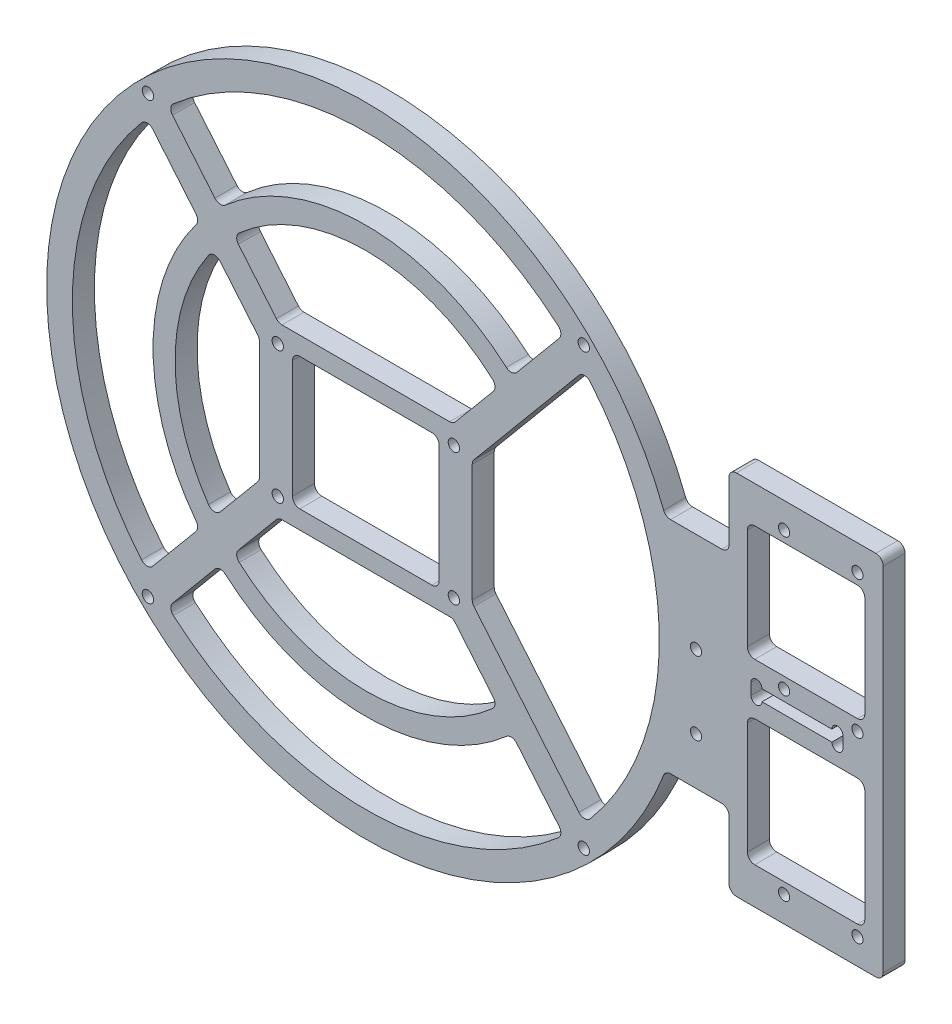
SolidWorks part; units mm, degrees
material "Thornel Mat VMA"
ref_plane "前视基准面" through (0, 0, 0) normal (0, 0, 1) x (1, 0, 0)
ref_plane "上视基准面" through (0, 0, 0) normal (0, 1, 0) x (1, 0, 0)
ref_plane "右视基准面" through (0, 0, 0) normal (1, 0, 0) x (0, 0, -1)
other "Configuration Table"
sketch "草图1" plane through (0, 0, 0) normal (0, 0, 1) x (1, 0, 0)
  line L1 (-24, -18) -> (24, -18) construction
  line L2 (-24, -18) -> (-24, 18) construction
  line L3 (-24, 18) -> (24, 18) construction
  line L4 (24, -18) -> (24, 18) construction
  line L5 (-24, -18) -> (24, 18) construction
  line L6 (-24, 18) -> (24, -18) construction
  circle A0 centre (24, 18) radius 1.55
  circle A1 centre (-24, 18) radius 1.55
  circle A2 centre (-24, -18) radius 1.55
  circle A3 centre (24, -18) radius 1.55
  circle A4 centre (0, 0) radius 87
  point P0 (0, 0)
  dimension "D3" = 3.1
  dimension "D4" = 174
  dimension "D1" = 48
  dimension "D2" = 36
extrude "凸台-拉伸1" add sketch "草图1" along normal blind 6
sketch "草图2" plane through (0, 0, 6) normal (0, 0, 1) x (1, 0, 0)
  line L0 (0, 87) -> (0, 0) construction
  line L1 (0, 0) -> (59.397, 59.397) construction
  circle A0 centre (0, 0) radius 84 construction
  circle A1 centre (0, 0) radius 87 construction
  circle A2 centre (59.397, 59.397) radius 1.55
  circle A3 centre (59.397, -59.397) radius 1.55
  circle A4 centre (-59.397, -59.397) radius 1.55
  circle A5 centre (-59.397, 59.397) radius 1.55
  point P17 (0, 0)
  dimension "D1" = 3
  dimension "D3" = 3.1
  dimension "D2" = 45
  dimension "D4" = 4
extrude "切除-拉伸1" cut sketch "草图2" against normal blind 40
sketch "草图3" plane through (0, 0, 6) normal (0, 0, 1) x (1, 0, 0)
  line L0 (0, 0) -> (87, 0) construction
  line L1 (37, -30) -> (137, -30)
  line L2 (37, -30) -> (37, 30)
  line L3 (37, 30) -> (137, 30)
  line L4 (137, -30) -> (137, 30)
  line L5 (37, -30) -> (137, 30) construction
  line L6 (37, 30) -> (137, -30) construction
  circle A0 centre (0, 0) radius 87 construction
  point P0 (87, 0)
  dimension "D1" = 60
  dimension "D2" = 100
extrude "凸台-拉伸2" add sketch "草图3" against normal up to surface (6 mm away) up to face at (-57.847, 59.397, 0)
sketch "草图4" plane through (0, 0, 0) normal (0, 0, -1) x (-1, 0, 0)
  line L0 (-59.397, 59.397) -> (-29, 23) construction
  line L1 (-29, -23) -> (29, -23)
  line L2 (-29, -23) -> (-29, 23)
  line L3 (-29, 23) -> (29, 23)
  line L4 (29, -23) -> (29, 23)
  line L5 (-29, -23) -> (29, 23) construction
  line L6 (-29, 23) -> (29, -23) construction
  line L7 (-29, -23) -> (-59.397, -59.397) construction
  line L8 (29, -23) -> (59.397, -59.397) construction
  line L9 (29, 23) -> (59.397, 59.397) construction
  line L10 (-59.585, 53.3819) -> (-29, 16.7598)
  line L11 (-53.9292, 59.0901) -> (-23.7885, 23)
  line L12 (0, 0) -> (0, 97.9408) construction
  line L13 (53.9292, 59.0901) -> (23.7885, 23)
  line L14 (59.585, 53.3819) -> (29, 16.7598)
  line L15 (0, 0) -> (125.7925, 0) construction
  line L16 (-59.585, -53.3819) -> (-29, -16.7598)
  line L17 (-53.9292, -59.0901) -> (-23.7885, -23)
  line L18 (59.585, -53.3819) -> (29, -16.7598)
  line L19 (53.9292, -59.0901) -> (23.7885, -23)
  circle A0 centre (0, 0) radius 80
  circle A2 centre (0, 0) radius 84 construction
  circle A3 centre (24, 18) radius 1.55 construction
  dimension "D1" = 4
  dimension "D2" = 5
  dimension "D3" = 5
  dimension "D4" = 4
extrude "切除-拉伸2" cut sketch "草图4" against normal blind 40 contours L17 A0 L19 L1 | L18 A0 L14 L4 | L10 A0 L16 L2 | L13 A0 L11 L3
sketch "草图5" plane through (0, 0, 0) normal (0, 0, -1) x (-1, 0, 0)
  circle A0 centre (0, 0) radius 55 construction
  arc A1 (59.585, -53.3819) -> (59.585, 53.3819) centre (0, 0) ccw construction
  circle A2 centre (0, 0) radius 58
  circle A3 centre (0, 0) radius 52
  dimension "D1" = 25
  dimension "D2" = 3
  dimension "D3" = 3
extrude "凸台-拉伸3" add sketch "草图5" against normal up to surface (6 mm away) up to face at (67.166, 0, 6)
sketch "草图6" plane through (0, 0, 0) normal (0, 0, -1) x (-1, 0, 0)
  line L0 (-45.2767, 36.2494) -> (-41.3432, 31.5395)
  line L1 (-41.3432, 31.5395) -> (-41.3432, -31.5395)
  line L2 (-41.3432, -31.5395) -> (-45.2767, -36.2494)
  arc A0 (-41.3432, 31.5395) -> (-41.3432, -31.5395) centre (0, 0) ccw construction
  arc A1 (-45.2767, 36.2494) -> (-45.2767, -36.2494) centre (0, 0) ccw construction
  arc A2 (-45.2767, 36.2494) -> (-45.2767, -36.2494) centre (0, 0) ccw
extrude "切除-拉伸3" cut sketch "草图6" against normal blind 70
fillet "圆角2" radius 2 28 edges at (35.9543, -37.5671, 3) (-35.9543, -37.5671, 3) (-41.3432, -31.5395, 3) (-29, -16.7598, 3) (-29, 16.7598, 3) (-41.3432, 31.5395, 3) (-35.9543, 37.5671, 3) (-23.7885, 23, 3) (23.7885, 23, 3) (35.9543, 37.5671, 3) (-53.9292, -59.0901, 3) (53.9292, -59.0901, 3) (39.8082, -42.1818, 3) (-39.8082, -42.1818, 3) (-59.585, 53.3819, 3) (-59.585, -53.3819, 3) (-45.2767, -36.2494, 3) (-45.2767, 36.2494, 3) (53.9292, 59.0901, 3) (-53.9292, 59.0901, 3) (-39.8082, 42.1818, 3) (39.8082, 42.1818, 3) (29, 16.7598, 3) (29, -16.7598, 3) (59.585, -53.3819, 3) (59.585, 53.3819, 3) (-23.7885, -23, 3) (23.7885, -23, 3)
sketch "草图7" plane through (0, 0, 0) normal (0, 0, -1) x (-1, 0, 0)
  line L0 (-118, 0) -> (0, 0) construction
  line L1 (-137, -50) -> (-99, -50)
  line L2 (-137, -50) -> (-137, 50)
  line L3 (-137, 50) -> (-99, 50)
  line L4 (-99, -50) -> (-99, 50)
  line L5 (-137, -50) -> (-99, 50) construction
  line L6 (-137, 50) -> (-99, -50) construction
  line L7 (-137, 30) -> (-137, -30) construction
  point P0 (-118, 0)
  dimension "D1" = 100
  dimension "D2" = 38
extrude "凸台-拉伸4" add sketch "草图7" against normal up to surface (6 mm away) contours L2 L1 L4 L3 up to face at (46.7508, 0, 6)
sketch "草图8" plane through (0, 0, 0) normal (0, 0, -1) x (-1, 0, 0)
  line L0 (-22.8531, 23) -> (22.8531, 23) construction
  line L1 (-20, -18) -> (20, -18)
  line L2 (-20, -18) -> (-20, 18)
  line L3 (-20, 18) -> (20, 18)
  line L4 (20, -18) -> (20, 18)
  line L5 (-20, -18) -> (20, 18) construction
  line L6 (-20, 18) -> (20, -18) construction
  circle A0 centre (24, 18) radius 1.55 construction
  point P0 (0, 0)
  dimension "D1" = 4
  dimension "D2" = 5
extrude "切除-拉伸4" cut sketch "草图8" against normal mid plane 40
fillet "圆角3" radius 2 4 edges at (-20, -18, 3) (-20, 18, 3) (20, -18, 3) (20, 18, 3)
sketch "草图9" plane through (0, 0, 0) normal (0, 0, -1) x (-1, 0, 0)
  line L0 (-137, 0) -> (-107.301, 0) construction
  line L1 (-137, 50) -> (-137, -50) construction
  circle A0 centre (-114, -43) radius 1.5 construction
  circle A1 centre (-134, -43) radius 1.5 construction
  circle A2 centre (-114, -43) radius 1.5 construction
  circle A3 centre (-134, -43) radius 1.5 construction
  circle A4 centre (-134, -43) radius 1.525
  circle A5 centre (-114, -43) radius 1.525
  circle A6 centre (-114, 43) radius 1.525
  circle A7 centre (-134, 43) radius 1.525
  dimension "D1" = 3.05
extrude "切除-拉伸5" cut sketch "草图9" against normal blind 80
sketch "草图10" plane through (0, 0, 6) normal (0, 0, 1) x (1, 0, 0)
  circle A0 centre (90, 2.881) radius 1.5 construction
  circle A1 centre (90, -17.119) radius 1.5 construction
  circle A2 centre (90, 2.881) radius 1.5 construction
  circle A3 centre (90, -17.119) radius 1.5 construction
  circle A4 centre (90, -17.119) radius 1.525
  circle A5 centre (90, 2.881) radius 1.525
  dimension "D1" = 3.05
extrude "切除-拉伸6" cut sketch "草图10" against normal blind 80
sketch "草图11" plane through (0, 0, 0) normal (0, 0, -1) x (-1, 0, 0)
  line L0 (-104.97, -0.5402) -> (-104.97, 2.5198)
  line L1 (-104.97, 2.5198) -> (-130.03, 2.5198)
  line L2 (-130.03, 2.5198) -> (-130.03, -0.5402)
  line L3 (-130.03, -0.5402) -> (-104.97, -0.5402)
  line L4 (-105, -0.5102) -> (-105, 2.4898)
  line L5 (-130, -0.5102) -> (-105, -0.5102)
  line L6 (-130, 2.4898) -> (-130, -0.5102)
  line L7 (-105, 2.4898) -> (-130, 2.4898)
  line L8 (-105, -0.5102) -> (-105, 2.4898) construction
  line L9 (-130, -0.5102) -> (-105, -0.5102) construction
  line L10 (-130, 2.4898) -> (-130, -0.5102) construction
  line L11 (-105, 2.4898) -> (-130, 2.4898) construction
  dimension "D1" = 0
  dimension "D2" = 0.03
extrude "切除-拉伸7" cut sketch "草图11" against normal blind 30
sketch "草图12" plane through (0, 0, 0) normal (0, 0, -1) x (-1, 0, 0)
  line L0 (-104.97, 2.5198) -> (-130.03, 2.5198) construction
  line L1 (-130.03, -0.5402) -> (-104.97, -0.5402) construction
  circle A0 centre (-128.525, 2.5198) radius 1.505
  circle A1 centre (-128.525, -0.5402) radius 1.505
  circle A2 centre (-106.475, 2.5198) radius 1.505
  circle A3 centre (-106.475, -0.5402) radius 1.505
  dimension "D1" = 3.01
extrude "切除-拉伸8" cut sketch "草图12" against normal blind 60
sketch "草图13" plane through (0, 0, 0) normal (0, 0, -1) x (-1, 0, 0)
  line L0 (-137, -50) -> (-99, -50) construction
  line L1 (-137, 50) -> (-141, 50)
  line L2 (-137, 50) -> (-137, -50)
  line L3 (-137, -50) -> (-141, -50)
  line L4 (-141, 50) -> (-141, -50)
  dimension "D1" = 4
extrude "凸台-拉伸5" add sketch "草图13" against normal up to surface (6 mm away) up to face at (117.5, 0.9898, 6)
sketch "草图14" plane through (0, 0, 0) normal (0, 0, -1) x (-1, 0, 0)
  circle A0 centre (-114, 5.4898) radius 1.5 construction
  circle A1 centre (-134, 5.4898) radius 1.5
  circle A2 centre (-134, 5.4898) radius 1.5 construction
  circle A3 centre (-114, 5.4898) radius 1.5 construction
  circle A4 centre (-134, 5.4898) radius 1.525
  circle A5 centre (-114, 5.4898) radius 1.525
  dimension "D2" = 3.05
  dimension "D1" = 0
extrude "切除-拉伸9" cut sketch "草图14" against normal up to surface (6 mm away) up to face at (117.5, 0.9898, 6)
sketch "草图15" plane through (0, 0, 6) normal (0, 0, 1) x (1, 0, 0)
  line L0 (141, 50) -> (141, -50) construction
  line L1 (104, 8.4898) -> (136, 8.4898)
  line L2 (104, 8.4898) -> (104, 40)
  line L3 (104, 40) -> (136, 40)
  line L4 (136, 8.4898) -> (136, 40)
  line L5 (104, 8.4898) -> (136, 40) construction
  line L6 (104, 40) -> (136, 8.4898) construction
  line L7 (99, 30) -> (99, 50) construction
  line L9 (104, -40) -> (136, -40)
  line L10 (104, -40) -> (104, -5.5402)
  line L11 (104, -5.5402) -> (136, -5.5402)
  line L12 (136, -40) -> (136, -5.5402)
  line L13 (104, -40) -> (136, -5.5402) construction
  line L14 (104, -5.5402) -> (136, -40) construction
  circle A0 centre (134, 43) radius 1.525 construction
  circle A1 centre (134, 5.4898) radius 1.525 construction
  arc A2 (127.02, -0.5402) -> (130.03, -0.5402) centre (128.525, -0.5402) ccw construction
  circle A3 centre (134, -43) radius 1.525 construction
  point P0 (120, 24.2449)
  point P13 (120, -22.7701)
  dimension "D1" = 3
  dimension "D2" = 3
  dimension "D3" = 5
  dimension "D4" = 5
  dimension "D5" = 5
  dimension "D6" = 3
extrude "切除-拉伸10" cut sketch "草图15" against normal up to surface (6 mm away) up to face at (132.475, 5.4898, 0)
fillet "圆角4" radius 2 16 edges at (81.6639, -30, 3) (81.6639, 30, 3) (99, 30, 3) (99, 50, 3) (141, 50, 3) (99, -30, 3) (136, -5.5402, 3) (104, -5.5402, 3) (104, -40, 3) (136, -40, 3) (136, 40, 3) (104, 40, 3) (104, 8.4898, 3) (136, 8.4898, 3) (99, -50, 3) (141, -50, 3)
equation "\"D2@草图4\"=\"D3@草图4\""
equation "\"D3@草图5\"=\"D2@草图5\""
